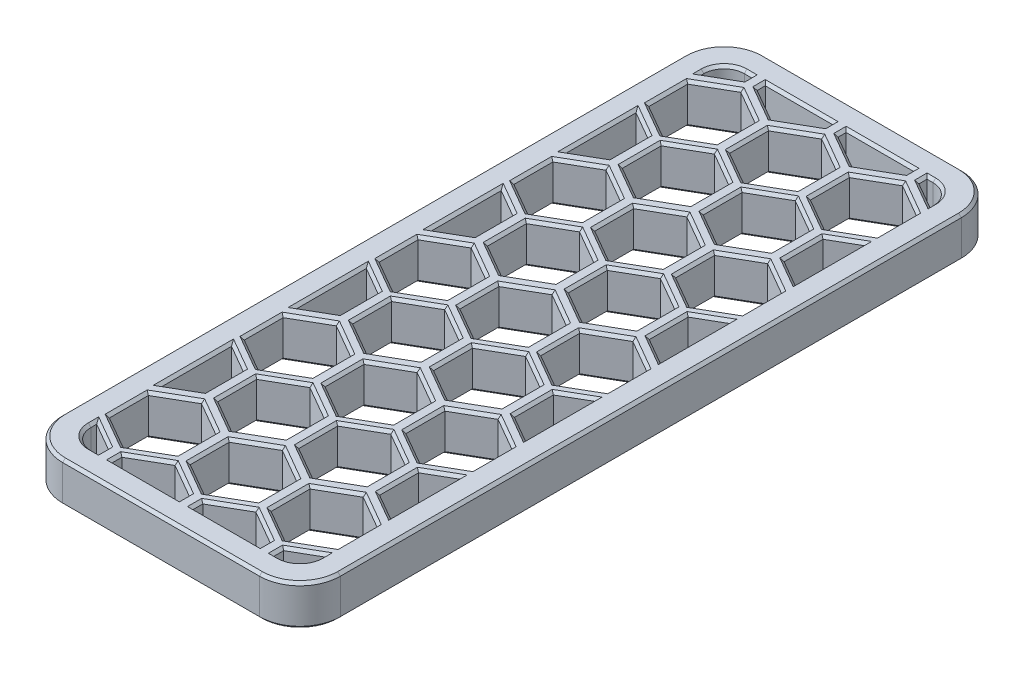
SolidWorks part; units mm, degrees
ref_plane "Front Plane" through (0, 0, 0) normal (0, 0, 1) x (1, 0, 0)
ref_plane "Top Plane" through (0, 0, 0) normal (0, 1, 0) x (1, 0, 0)
ref_plane "Right Plane" through (0, 0, 0) normal (1, 0, 0) x (0, 0, -1)
sketch "Sketch1" plane through (0, 0, 0) normal (0, 1, 0) x (1, 0, 0)
  line L1 (-68.5, 30) -> (68.5, 30)
  line L2 (-68.5, 30) -> (-68.5, -30)
  line L3 (-68.5, -30) -> (68.5, -30)
  line L4 (68.5, 30) -> (68.5, -30)
  line L5 (-68.5, 30) -> (68.5, -30) construction
  line L6 (-68.5, -30) -> (68.5, 30) construction
  point P0 (0, 0)
  dimension "D1" = 60
  dimension "D2" = 137
extrude "Boss-Extrude1" add sketch "Sketch1" along normal blind 6.5
sketch "Sketch2" plane through (0, 6.5, 0) normal (0, 1, 0) x (1, 0, 0)
  line L0 (0, 0) -> (47.9381, 0) construction
  line L1 (68.5, -30) -> (68.5, 30) construction
  line L2 (-36.5, 27.75) -> (64.5, 27.75)
  line L3 (-36.5, 27.75) -> (-36.5, -27.75)
  line L4 (-36.5, -27.75) -> (64.5, -27.75)
  line L5 (64.5, 27.75) -> (64.5, -27.75)
  line L6 (-36.5, 27.75) -> (64.5, -27.75) construction
  line L7 (-36.5, -27.75) -> (64.5, 27.75) construction
  point P3 (14, 0)
  dimension "D1" = 55.5
  dimension "D2" = 101
  dimension "D3" = 4
extrude "Cut-Extrude1" cut sketch "Sketch2" against normal blind 1.65
sketch "Sketch3" plane through (0, 4.85, 0) normal (0, 1, 0) x (1, 0, 0)
  line L0 (64.5, -27.75) -> (64.5, 27.75) construction
  line L1 (57.35, -27.75) -> (-29.95, -27.75)
  line L2 (57.35, -27.75) -> (57.35, 27.75)
  line L3 (57.35, 27.75) -> (-29.95, 27.75)
  line L4 (-29.95, -27.75) -> (-29.95, 27.75)
  line L5 (64.5, 27.75) -> (-36.5, 27.75) construction
  dimension "D1" = 7.15
  dimension "D2" = 87.3
  dimension "D3" = 55.5
  dimension "D4" = 0
extrude "Cut-Extrude2" cut sketch "Sketch3" against normal blind 4.1
sketch "Sketch4" plane through (0, 0.75, 0) normal (0, 1, 0) x (1, 0, 0)
  line L0 (0, 0) -> (36.8123, 0) construction
  line L1 (64.5, -27.75) -> (64.5, 27.75) construction
  line L2 (-20.6, 25.85) -> (54.8, 25.85)
  line L3 (-20.6, 25.85) -> (-20.6, -25.85)
  line L4 (-20.6, -25.85) -> (54.8, -25.85)
  line L5 (54.8, 25.85) -> (54.8, -25.85)
  line L6 (-20.6, 25.85) -> (54.8, -25.85) construction
  line L7 (-20.6, -25.85) -> (54.8, 25.85) construction
  point P3 (17.1, 0)
  dimension "D1" = 51.7
  dimension "D2" = 75.4
  dimension "D3" = 9.7
extrude "Cut-Extrude3" cut sketch "Sketch4" against normal through all
fillet "Fillet1" radius 1 4 edges at (54.8, 0.375, -25.85) (54.8, 0.375, 25.85) (-20.6, 0.375, 25.85) (-20.6, 0.375, -25.85)
sketch "Sketch6" plane through (0, 4.85, 0) normal (0, 1, 0) x (1, 0, 0)
  line L0 (57.35, -27.75) -> (57.35, 27.75) construction
  line L1 (64.5, -27.75) -> (57.35, -27.75)
  line L2 (64.5, -27.75) -> (64.5, -19.75)
  line L3 (64.5, -19.75) -> (57.35, -19.75)
  line L4 (57.35, -27.75) -> (57.35, -19.75)
  line L5 (57.35, -27.75) -> (57.35, 27.75) construction
  line L6 (64.5, 27.75) -> (57.35, 27.75)
  line L7 (64.5, 27.75) -> (64.5, 19.75)
  line L8 (64.5, 19.75) -> (57.35, 19.75)
  line L9 (57.35, 27.75) -> (57.35, 19.75)
  line L10 (-29.95, 27.75) -> (-29.95, -27.75) construction
  line L11 (-36.5, 27.75) -> (-29.95, 27.75)
  line L12 (-36.5, 27.75) -> (-36.5, 19.75)
  line L13 (-36.5, 19.75) -> (-29.95, 19.75)
  line L14 (-29.95, 27.75) -> (-29.95, 19.75)
  line L16 (-36.5, -27.75) -> (-29.95, -27.75)
  line L17 (-36.5, -27.75) -> (-36.5, -19.75)
  line L18 (-36.5, -19.75) -> (-29.95, -19.75)
  line L19 (-29.95, -27.75) -> (-29.95, -19.75)
  dimension "D1" = 8
  dimension "D2" = 8
  dimension "D3" = 8
  dimension "D4" = 8
extrude "Cut-Extrude4" cut sketch "Sketch6" against normal blind 2.5
fillet "Fillet2" radius 3 4 edges at (57.35, 3.6, -19.75) (57.35, 3.6, 19.75) (-29.95, 3.6, 19.75) (-29.95, 3.6, -19.75)
chamfer "Chamfer1" distance 0.5 angle 45 8 edges at (17.1, 0, -25.85) (-20.3071, 0, -25.5571) (54.5071, 0, -25.5571) (-20.6, 0, 0) (54.8, 0, 0) (-20.3071, 0, 25.5571) (54.5071, 0, 25.5571) (17.1, 0, 25.85)
sketch "Sketch7" plane through (0, 6.5, 0) normal (0, 1, 0) x (1, 0, 0)
  line L0 (0, 0) -> (-52.5, 0) construction
  line L1 (-36.5, 27.75) -> (-36.5, -27.75) construction
  line L2 (-63, 26.2268) -> (-42, 26.2268)
  line L3 (-63, 26.2268) -> (-63, -26.2268)
  line L4 (-63, -26.2268) -> (-42, -26.2268)
  line L5 (-42, 26.2268) -> (-42, -26.2268)
  line L6 (-63, 26.2268) -> (-42, -26.2268) construction
  line L7 (-63, -26.2268) -> (-42, 26.2268) construction
  line L8 (-68.5, 30) -> (-68.5, -30) construction
  dimension "D1" = 5.5
  dimension "D2" = 5.5
extrude "Cut-Extrude5" cut sketch "Sketch7" against normal through all
fillet "Fillet3" radius 3 4 edges at (-42, 3.25, 26.2268) (-63, 3.25, 26.2268) (-63, 3.25, -26.2268) (-42, 3.25, -26.2268)
fillet "Fillet5" radius 2 10 edges at (62.425, 4.85, 19.75) (58.2287, 4.85, 18.8713) (62.425, 4.85, -19.75) (58.2287, 4.85, -18.8713) (-34.725, 4.85, -19.75) (-30.8287, 4.85, -18.8713) (-34.725, 4.85, 19.75) (-30.8287, 4.85, 18.8713) (57.35, 4.85, 0) (-29.95, 4.85, 0)
chamfer "Chamfer3" distance 1 angle 45 4 edges at (57.35, 2.35, -22.25) (57.35, 2.35, 22.25) (-29.95, 2.35, 22.25) (-29.95, 2.35, -22.25)
fillet "Fillet6" radius 1.5 4 edges at (68.5, 3.25, 30) (-68.5, 3.25, 30) (-68.5, 3.25, -30) (68.5, 3.25, -30)
fillet "Fillet7" radius 1 16 edges at (-68.0607, 0, 29.5607) (-68.5, 0, 0) (-68.0607, 0, -29.5607) (0, 0, -30) (68.0607, 0, -29.5607) (68.5, 0, 0) (68.0607, 0, 29.5607) (-62.1213, 0, -25.3481) (-52.5, 0, -26.2268) (-42.8787, 0, -25.3481) (-42, 0, 0) (-42.8787, 0, 25.3481) (-52.5, 0, 26.2268) (-62.1213, 0, 25.3481) (0, 0, 30) (-63, 0, 0)
sketch "Sketch8" plane through (0, 0, 0) normal (0, -1, 0) x (1, 0, 0)
  line L28 (-45, 26.0268) -> (-60, 26.0268)
  line L29 (-42.2, -23.2268) -> (-42.2, 23.2268)
  line L30 (-60, -26.0268) -> (-45, -26.0268)
  line L31 (-62.8, 23.2268) -> (-62.8, -23.2268)
  line L32 (-45, 26.0268) -> (-60, 26.0268)
  line L33 (-42.2, -23.2268) -> (-42.2, 23.2268)
  line L34 (-60, -26.0268) -> (-45, -26.0268)
  line L35 (-62.8, 23.2268) -> (-62.8, -23.2268)
  arc A24 (-60, 26.0268) -> (-62.8, 23.2268) centre (-60, 23.2268) ccw
  arc A25 (-42.2, 23.2268) -> (-45, 26.0268) centre (-45, 23.2268) ccw
  arc A26 (-45, -26.0268) -> (-42.2, -23.2268) centre (-45, -23.2268) ccw
  arc A27 (-62.8, -23.2268) -> (-60, -26.0268) centre (-60, -23.2268) ccw
  arc A28 (-60, 26.0268) -> (-62.8, 23.2268) centre (-60, 23.2268) ccw
  arc A29 (-42.2, 23.2268) -> (-45, 26.0268) centre (-45, 23.2268) ccw
  arc A30 (-45, -26.0268) -> (-42.2, -23.2268) centre (-45, -23.2268) ccw
  arc A31 (-62.8, -23.2268) -> (-60, -26.0268) centre (-60, -23.2268) ccw
  dimension "D1" = 0.2
extrude "Boss-Extrude2" add sketch "Sketch8" along normal blind 10 separate body
sketch "Sketch9" plane through (-62.8, 0, 0) normal (-1, 0, 0) x (0, 0, 1)
  line L0 (23.2268, -10) -> (-23.2268, -10) construction
  line L1 (-34.3894, 13.8504) -> (38.8639, 13.8504)
  line L2 (-34.3894, 13.8504) -> (-34.3894, -7)
  line L3 (-34.3894, -7) -> (38.8639, -7)
  line L4 (38.8639, 13.8504) -> (38.8639, -7)
  dimension "D1" = 3
extrude "Cut-Extrude6" cut sketch "Sketch9" against normal through all and the other way through all
sketch "Sketch10" plane through (0, -10, 0) normal (0, -1, 0) x (1, 0, 0)
  line L0 (-52.4279, 17.1053) -> (-49.9279, 18.5487)
  line L1 (-58.4279, 17.1006) -> (-55.9279, 18.544)
  line L2 (-55.9279, 18.544) -> (-55.9279, 21.4307)
  line L3 (-55.9279, 21.4307) -> (-58.4279, 22.8741)
  line L4 (-58.4279, 22.8741) -> (-60.9279, 21.4307)
  line L5 (-60.9279, 21.4307) -> (-60.9279, 18.544)
  line L6 (-60.9279, 18.544) -> (-58.4279, 17.1006)
  line L7 (-49.9279, 18.5487) -> (-49.9279, 21.4354)
  line L8 (-49.9279, 21.4354) -> (-52.4279, 22.8788)
  line L9 (-52.4279, 22.8788) -> (-54.9279, 21.4354)
  line L10 (-54.9279, 21.4354) -> (-54.9279, 18.5487)
  line L11 (-54.9279, 18.5487) -> (-52.4279, 17.1053)
  line L12 (-46.4279, 17.1086) -> (-43.9279, 18.552)
  line L13 (-43.9279, 18.552) -> (-43.9279, 21.4387)
  line L14 (-43.9279, 21.4387) -> (-46.4279, 22.8821)
  line L15 (-46.4279, 22.8821) -> (-48.9279, 21.4387)
  line L16 (-48.9279, 21.4387) -> (-48.9279, 18.552)
  line L17 (-48.9279, 18.552) -> (-46.4279, 17.1086)
  line L18 (-58.4279, 7.1006) -> (-55.9279, 8.544)
  line L19 (-55.9279, 8.544) -> (-55.9279, 11.4307)
  line L20 (-55.4437, 12.0459) -> (-52.9437, 13.4893)
  line L21 (-52.9437, 13.4893) -> (-52.9437, 16.376)
  line L22 (-52.9437, 16.376) -> (-55.4437, 17.8194)
  line L23 (-55.4437, 17.8194) -> (-57.9437, 16.376)
  line L24 (-57.9437, 16.376) -> (-57.9437, 13.4893)
  line L25 (-57.9437, 13.4893) -> (-55.4437, 12.0459)
  line L26 (-55.9279, 11.4307) -> (-58.4279, 12.8741)
  line L27 (-58.4279, 12.8741) -> (-60.9279, 11.4307)
  line L28 (-60.9279, 11.4307) -> (-60.9279, 8.544)
  line L29 (-60.9279, 8.544) -> (-58.4279, 7.1006)
  line L30 (-52.4279, 7.1053) -> (-49.9279, 8.5487)
  line L31 (-49.9279, 8.5487) -> (-49.9279, 11.4354)
  line L32 (-49.9279, 11.4354) -> (-52.4279, 12.8788)
  line L33 (-52.4279, 12.8788) -> (-54.9279, 11.4354)
  line L34 (-54.9279, 11.4354) -> (-54.9279, 8.5487)
  line L35 (-54.9279, 8.5487) -> (-52.4279, 7.1053)
  line L36 (-46.4279, 7.1086) -> (-43.9279, 8.552)
  line L37 (-43.9279, 8.552) -> (-43.9279, 11.4387)
  line L38 (-43.9279, 11.4387) -> (-46.4279, 12.8821)
  line L39 (-46.4279, 12.8821) -> (-48.9279, 11.4387)
  line L40 (-48.9279, 11.4387) -> (-48.9279, 8.552)
  line L41 (-48.9279, 8.552) -> (-46.4279, 7.1086)
  line L42 (-58.4279, -2.8994) -> (-55.9279, -1.456)
  line L43 (-55.9279, -1.456) -> (-55.9279, 1.4307)
  line L44 (-55.9279, 1.4307) -> (-58.4279, 2.8741)
  line L45 (-58.4279, 2.8741) -> (-60.9279, 1.4307)
  line L46 (-60.9279, 1.4307) -> (-60.9279, -1.456)
  line L47 (-60.9279, -1.456) -> (-58.4279, -2.8994)
  line L48 (-52.4279, -2.8947) -> (-49.9279, -1.4513)
  line L49 (-49.9279, -1.4513) -> (-49.9279, 1.4354)
  line L50 (-49.9279, 1.4354) -> (-52.4279, 2.8788)
  line L51 (-52.4279, 2.8788) -> (-54.9279, 1.4354)
  line L52 (-54.9279, 1.4354) -> (-54.9279, -1.4513)
  line L53 (-54.9279, -1.4513) -> (-52.4279, -2.8947)
  line L54 (-46.4279, -2.8914) -> (-43.9279, -1.448)
  line L55 (-43.9279, -1.448) -> (-43.9279, 1.4387)
  line L56 (-43.9279, 1.4387) -> (-46.4279, 2.8821)
  line L57 (-46.4279, 2.8821) -> (-48.9279, 1.4387)
  line L58 (-48.9279, 1.4387) -> (-48.9279, -1.448)
  line L59 (-48.9279, -1.448) -> (-46.4279, -2.8914)
  line L60 (-58.4279, -12.8994) -> (-55.9279, -11.456)
  line L61 (-55.9279, -11.456) -> (-55.9279, -8.5693)
  line L62 (-55.9279, -8.5693) -> (-58.4279, -7.1259)
  line L63 (-58.4279, -7.1259) -> (-60.9279, -8.5693)
  line L64 (-60.9279, -8.5693) -> (-60.9279, -11.456)
  line L65 (-60.9279, -11.456) -> (-58.4279, -12.8994)
  line L66 (-52.4279, -12.8947) -> (-49.9279, -11.4513)
  line L67 (-49.9279, -11.4513) -> (-49.9279, -8.5646)
  line L68 (-49.9279, -8.5646) -> (-52.4279, -7.1212)
  line L69 (-52.4279, -7.1212) -> (-54.9279, -8.5646)
  line L70 (-54.9279, -8.5646) -> (-54.9279, -11.4513)
  line L71 (-54.9279, -11.4513) -> (-52.4279, -12.8947)
  line L72 (-46.4279, -12.8914) -> (-43.9279, -11.448)
  line L73 (-43.9279, -11.448) -> (-43.9279, -8.5613)
  line L74 (-43.9279, -8.5613) -> (-46.4279, -7.1179)
  line L75 (-46.4279, -7.1179) -> (-48.9279, -8.5613)
  line L76 (-48.9279, -8.5613) -> (-48.9279, -11.448)
  line L77 (-48.9279, -11.448) -> (-46.4279, -12.8914)
  line L78 (-58.4279, -22.8994) -> (-55.9279, -21.456)
  line L79 (-55.9279, -21.456) -> (-55.9279, -18.5693)
  line L80 (-55.9279, -18.5693) -> (-58.4279, -17.1259)
  line L81 (-58.4279, -17.1259) -> (-60.9279, -18.5693)
  line L82 (-60.9279, -18.5693) -> (-60.9279, -21.456)
  line L83 (-60.9279, -21.456) -> (-58.4279, -22.8994)
  line L84 (-52.4279, -22.8947) -> (-49.9279, -21.4513)
  line L85 (-49.9279, -21.4513) -> (-49.9279, -18.5646)
  line L86 (-49.9279, -18.5646) -> (-52.4279, -17.1212)
  line L87 (-52.4279, -17.1212) -> (-54.9279, -18.5646)
  line L88 (-54.9279, -18.5646) -> (-54.9279, -21.4513)
  line L89 (-54.9279, -21.4513) -> (-52.4279, -22.8947)
  line L90 (-46.4279, -22.8914) -> (-43.9279, -21.448)
  line L91 (-43.9279, -21.448) -> (-43.9279, -18.5613)
  line L92 (-43.9279, -18.5613) -> (-46.4279, -17.1179)
  line L93 (-46.4279, -17.1179) -> (-48.9279, -18.5613)
  line L94 (-48.9279, -18.5613) -> (-48.9279, -21.448)
  line L95 (-48.9279, -21.448) -> (-46.4279, -22.8914)
  line L96 (-55.4437, 2.0459) -> (-52.9437, 3.4893)
  line L97 (-52.9437, 3.4893) -> (-52.9437, 6.376)
  line L98 (-52.9437, 6.376) -> (-55.4437, 7.8194)
  line L99 (-55.4437, 7.8194) -> (-57.9437, 6.376)
  line L100 (-57.9437, 6.376) -> (-57.9437, 3.4893)
  line L101 (-57.9437, 3.4893) -> (-55.4437, 2.0459)
  line L102 (-55.4437, -7.9541) -> (-52.9437, -6.5107)
  line L103 (-52.9437, -6.5107) -> (-52.9437, -3.624)
  line L104 (-52.9437, -3.624) -> (-55.4437, -2.1806)
  line L105 (-55.4437, -2.1806) -> (-57.9437, -3.624)
  line L106 (-57.9437, -3.624) -> (-57.9437, -6.5107)
  line L107 (-57.9437, -6.5107) -> (-55.4437, -7.9541)
  line L108 (-55.4437, -17.9541) -> (-52.9437, -16.5107)
  line L109 (-52.9437, -16.5107) -> (-52.9437, -13.624)
  line L110 (-52.9437, -13.624) -> (-55.4437, -12.1806)
  line L111 (-55.4437, -12.1806) -> (-57.9437, -13.624)
  line L112 (-57.9437, -13.624) -> (-57.9437, -16.5107)
  line L113 (-57.9437, -16.5107) -> (-55.4437, -17.9541)
  line L114 (-55.4437, -27.9541) -> (-52.9437, -26.5107)
  line L115 (-52.9437, -26.5107) -> (-52.9437, -23.624)
  line L116 (-52.9437, -23.624) -> (-55.4437, -22.1806)
  line L117 (-55.4437, -22.1806) -> (-57.9437, -23.624)
  line L118 (-57.9437, -23.624) -> (-57.9437, -26.5107)
  line L119 (-57.9437, -26.5107) -> (-55.4437, -27.9541)
  line L120 (-55.4437, 12.0459) -> (-52.9437, 13.4893)
  line L121 (-52.9437, 13.4893) -> (-52.9437, 16.376)
  line L122 (-52.9437, 16.376) -> (-55.4437, 17.8194)
  line L123 (-55.4437, 17.8194) -> (-57.9437, 16.376)
  line L124 (-57.9437, 16.376) -> (-57.9437, 13.4893)
  line L125 (-57.9437, 13.4893) -> (-55.4437, 12.0459)
  line L126 (-55.4437, 2.0459) -> (-52.9437, 3.4893)
  line L127 (-52.9437, 3.4893) -> (-52.9437, 6.376)
  line L128 (-52.9437, 6.376) -> (-55.4437, 7.8194)
  line L129 (-55.4437, 7.8194) -> (-57.9437, 6.376)
  line L130 (-57.9437, 6.376) -> (-57.9437, 3.4893)
  line L131 (-57.9437, 3.4893) -> (-55.4437, 2.0459)
  line L132 (-55.4437, -7.9541) -> (-52.9437, -6.5107)
  line L133 (-52.9437, -6.5107) -> (-52.9437, -3.624)
  line L134 (-52.9437, -3.624) -> (-55.4437, -2.1806)
  line L135 (-55.4437, -2.1806) -> (-57.9437, -3.624)
  line L136 (-57.9437, -3.624) -> (-57.9437, -6.5107)
  line L137 (-57.9437, -6.5107) -> (-55.4437, -7.9541)
  line L138 (-55.4437, -17.9541) -> (-52.9437, -16.5107)
  line L139 (-52.9437, -16.5107) -> (-52.9437, -13.624)
  line L140 (-52.9437, -13.624) -> (-55.4437, -12.1806)
  line L141 (-55.4437, -12.1806) -> (-57.9437, -13.624)
  line L142 (-57.9437, -13.624) -> (-57.9437, -16.5107)
  line L143 (-57.9437, -16.5107) -> (-55.4437, -17.9541)
  line L144 (-55.4437, 22.0459) -> (-52.9437, 23.4893)
  line L145 (-52.9437, 23.4893) -> (-52.9437, 26.376)
  line L146 (-52.9437, 26.376) -> (-55.4437, 27.8194)
  line L147 (-55.4437, 27.8194) -> (-57.9437, 26.376)
  line L148 (-57.9437, 26.376) -> (-57.9437, 23.4893)
  line L149 (-57.9437, 23.4893) -> (-55.4437, 22.0459)
  line L150 (-49.4437, 22.0459) -> (-46.9437, 23.4893)
  line L151 (-46.9437, 23.4893) -> (-46.9437, 26.376)
  line L152 (-46.9437, 26.376) -> (-49.4437, 27.8194)
  line L153 (-49.4437, 27.8194) -> (-51.9437, 26.376)
  line L154 (-51.9437, 26.376) -> (-51.9437, 23.4893)
  line L155 (-51.9437, 23.4893) -> (-49.4437, 22.0459)
  line L156 (-49.4437, 12.0459) -> (-46.9437, 13.4893)
  line L157 (-46.9437, 13.4893) -> (-46.9437, 16.376)
  line L158 (-46.9437, 16.376) -> (-49.4437, 17.8194)
  line L159 (-49.4437, 17.8194) -> (-51.9437, 16.376)
  line L160 (-51.9437, 16.376) -> (-51.9437, 13.4893)
  line L161 (-51.9437, 13.4893) -> (-49.4437, 12.0459)
  line L162 (-49.4437, 2.0459) -> (-46.9437, 3.4893)
  line L163 (-46.9437, 3.4893) -> (-46.9437, 6.376)
  line L164 (-46.9437, 6.376) -> (-49.4437, 7.8194)
  line L165 (-49.4437, 7.8194) -> (-51.9437, 6.376)
  line L166 (-51.9437, 6.376) -> (-51.9437, 3.4893)
  line L167 (-51.9437, 3.4893) -> (-49.4437, 2.0459)
  line L168 (-49.4437, -7.9541) -> (-46.9437, -6.5107)
  line L169 (-46.9437, -6.5107) -> (-46.9437, -3.624)
  line L170 (-46.9437, -3.624) -> (-49.4437, -2.1806)
  line L171 (-49.4437, -2.1806) -> (-51.9437, -3.624)
  line L172 (-51.9437, -3.624) -> (-51.9437, -6.5107)
  line L173 (-51.9437, -6.5107) -> (-49.4437, -7.9541)
  line L174 (-49.4437, -17.9541) -> (-46.9437, -16.5107)
  line L175 (-46.9437, -16.5107) -> (-46.9437, -13.624)
  line L176 (-46.9437, -13.624) -> (-49.4437, -12.1806)
  line L177 (-49.4437, -12.1806) -> (-51.9437, -13.624)
  line L178 (-51.9437, -13.624) -> (-51.9437, -16.5107)
  line L179 (-51.9437, -16.5107) -> (-49.4437, -17.9541)
  line L180 (-49.4437, -27.9541) -> (-46.9437, -26.5107)
  line L181 (-46.9437, -26.5107) -> (-46.9437, -23.624)
  line L182 (-46.9437, -23.624) -> (-49.4437, -22.1806)
  line L183 (-49.4437, -22.1806) -> (-51.9437, -23.624)
  line L184 (-51.9437, -23.624) -> (-51.9437, -26.5107)
  line L185 (-51.9437, -26.5107) -> (-49.4437, -27.9541)
  line L186 (-43.4437, 22.0459) -> (-40.9437, 23.4893)
  line L187 (-40.9437, 23.4893) -> (-40.9437, 26.376)
  line L188 (-40.9437, 26.376) -> (-43.4437, 27.8194)
  line L189 (-43.4437, 27.8194) -> (-45.9437, 26.376)
  line L190 (-45.9437, 26.376) -> (-45.9437, 23.4893)
  line L191 (-45.9437, 23.4893) -> (-43.4437, 22.0459)
  line L192 (-43.4437, 12.0459) -> (-40.9437, 13.4893)
  line L193 (-40.9437, 13.4893) -> (-40.9437, 16.376)
  line L194 (-40.9437, 16.376) -> (-43.4437, 17.8194)
  line L195 (-43.4437, 17.8194) -> (-45.9437, 16.376)
  line L196 (-45.9437, 16.376) -> (-45.9437, 13.4893)
  line L197 (-45.9437, 13.4893) -> (-43.4437, 12.0459)
  line L198 (-43.4437, 2.0459) -> (-40.9437, 3.4893)
  line L199 (-40.9437, 3.4893) -> (-40.9437, 6.376)
  line L200 (-40.9437, 6.376) -> (-43.4437, 7.8194)
  line L201 (-43.4437, 7.8194) -> (-45.9437, 6.376)
  line L202 (-45.9437, 6.376) -> (-45.9437, 3.4893)
  line L203 (-45.9437, 3.4893) -> (-43.4437, 2.0459)
  line L204 (-43.4437, -7.9541) -> (-40.9437, -6.5107)
  line L205 (-40.9437, -6.5107) -> (-40.9437, -3.624)
  line L206 (-40.9437, -3.624) -> (-43.4437, -2.1806)
  line L207 (-43.4437, -2.1806) -> (-45.9437, -3.624)
  line L208 (-45.9437, -3.624) -> (-45.9437, -6.5107)
  line L209 (-45.9437, -6.5107) -> (-43.4437, -7.9541)
  line L210 (-43.4437, -17.9541) -> (-40.9437, -16.5107)
  line L211 (-40.9437, -16.5107) -> (-40.9437, -13.624)
  line L212 (-40.9437, -13.624) -> (-43.4437, -12.1806)
  line L213 (-43.4437, -12.1806) -> (-45.9437, -13.624)
  line L214 (-45.9437, -13.624) -> (-45.9437, -16.5107)
  line L215 (-45.9437, -16.5107) -> (-43.4437, -17.9541)
  line L216 (-43.4437, -27.9541) -> (-40.9437, -26.5107)
  line L217 (-40.9437, -26.5107) -> (-40.9437, -23.624)
  line L218 (-40.9437, -23.624) -> (-43.4437, -22.1806)
  line L219 (-43.4437, -22.1806) -> (-45.9437, -23.624)
  line L220 (-45.9437, -23.624) -> (-45.9437, -26.5107)
  line L221 (-45.9437, -26.5107) -> (-43.4437, -27.9541)
  line L222 (-61.4437, 22.0459) -> (-58.9437, 23.4893)
  line L223 (-58.9437, 23.4893) -> (-58.9437, 26.376)
  line L224 (-58.9437, 26.376) -> (-61.4437, 27.8194)
  line L225 (-61.4437, 27.8194) -> (-63.9437, 26.376)
  line L226 (-63.9437, 26.376) -> (-63.9437, 23.4893)
  line L227 (-63.9437, 23.4893) -> (-61.4437, 22.0459)
  line L228 (-61.4437, 12.0459) -> (-58.9437, 13.4893)
  line L229 (-58.9437, 13.4893) -> (-58.9437, 16.376)
  line L230 (-58.9437, 16.376) -> (-61.4437, 17.8194)
  line L231 (-61.4437, 17.8194) -> (-63.9437, 16.376)
  line L232 (-63.9437, 16.376) -> (-63.9437, 13.4893)
  line L233 (-63.9437, 13.4893) -> (-61.4437, 12.0459)
  line L234 (-61.4437, 2.0459) -> (-58.9437, 3.4893)
  line L235 (-58.9437, 3.4893) -> (-58.9437, 6.376)
  line L236 (-58.9437, 6.376) -> (-61.4437, 7.8194)
  line L237 (-61.4437, 7.8194) -> (-63.9437, 6.376)
  line L238 (-63.9437, 6.376) -> (-63.9437, 3.4893)
  line L239 (-63.9437, 3.4893) -> (-61.4437, 2.0459)
  line L240 (-61.4437, -7.9541) -> (-58.9437, -6.5107)
  line L241 (-58.9437, -6.5107) -> (-58.9437, -3.624)
  line L242 (-58.9437, -3.624) -> (-61.4437, -2.1806)
  line L243 (-61.4437, -2.1806) -> (-63.9437, -3.624)
  line L244 (-63.9437, -3.624) -> (-63.9437, -6.5107)
  line L245 (-63.9437, -6.5107) -> (-61.4437, -7.9541)
  line L246 (-61.4437, -17.9541) -> (-58.9437, -16.5107)
  line L247 (-58.9437, -16.5107) -> (-58.9437, -13.624)
  line L248 (-58.9437, -13.624) -> (-61.4437, -12.1806)
  line L249 (-61.4437, -12.1806) -> (-63.9437, -13.624)
  line L250 (-63.9437, -13.624) -> (-63.9437, -16.5107)
  line L251 (-63.9437, -16.5107) -> (-61.4437, -17.9541)
  line L252 (-61.4437, -27.9541) -> (-58.9437, -26.5107)
  line L253 (-58.9437, -26.5107) -> (-58.9437, -23.624)
  line L254 (-58.9437, -23.624) -> (-61.4437, -22.1806)
  line L255 (-61.4437, -22.1806) -> (-63.9437, -23.624)
  line L256 (-63.9437, -23.624) -> (-63.9437, -26.5107)
  line L257 (-63.9437, -26.5107) -> (-61.4437, -27.9541)
  circle A0 centre (-58.4279, 19.9873) radius 2.5 construction
  circle A1 centre (-52.4279, 19.992) radius 2.5 construction
  circle A2 centre (-46.4279, 19.9954) radius 2.5 construction
  circle A3 centre (-55.4437, 14.9326) radius 2.5 construction
  point P105 (0, 0)
  point P231 (0, 0)
  point P268 (0, 0)
  point P269 (-57.9437, 26.376)
  point P270 (-57.9437, 26.376)
  point P271 (0, 0)
  point P272 (0, 0)
  arc M259 (-60, 26.0268) -> (-62.8, 23.2268) centre (-60, 23.2268) ccw
  line M260 (-62.8, 23.2268) -> (-62.8, -23.2268)
  arc M261 (-62.8, -23.2268) -> (-60, -26.0268) centre (-60, -23.2268) ccw
  line M262 (-60, -26.0268) -> (-45, -26.0268)
  arc M263 (-45, -26.0268) -> (-42.2, -23.2268) centre (-45, -23.2268) ccw
  line M264 (-42.2, -23.2268) -> (-42.2, 23.2268)
  arc M265 (-42.2, 23.2268) -> (-45, 26.0268) centre (-45, 23.2268) ccw
  line M266 (-45, 26.0268) -> (-60, 26.0268)
  dimension "D1" = 5
  dimension "D2" = 5
  dimension "D3" = 1
  dimension "D4" = 5
  dimension "D5" = 1
  dimension "D6" = 5
  dimension "D7" = 5
  dimension "D8" = 5
  dimension "D9" = 2
  dimension "D10" = 3
  dimension "D11" = 2
extrude "Cut-Extrude7" cut sketch "Sketch10" against normal through all contours L226 L227 L223 L224 L225 M260 M259 M266 | L147 L148 L145 L146 M266 | L148 L149 L144 L145 M266 | L227 L222 L223 M260 M266 M259 | L154 L155 L150 L151 M266 | L190 L191 L186 M264 M265 M266 | L189 L190 L186 L187 L188 M266 M265 M264 | L153 L154 L151 L152 M266 | L16 L17 L12 L13 L14 L15 | L10 L11 L0 L7 L8 L9 | L5 L6 L1 L2 L3 L4 | L233 L228 L229 L230 L231 M260 | L232 L233 L231 M260 | L24 L25 L20 L21 L22 L23 | L160 L161 L156 L157 L158 L159 | L196 L197 L192 L194 L195 M264 | L193 L194 L192 M264 | L40 L41 L36 L37 L38 L39 | L34 L35 L30 L31 L32 L33 | L28 L29 L18 L19 L26 L27 | L239 L234 L235 L236 L237 M260 | L238 L239 L237 M260 | L244 L245 L243 M260 | L245 L240 L241 L242 L243 M260 | L46 L47 L42 L43 L44 L45 | L100 L101 L96 L97 L98 L99 | L166 L167 L162 L163 L164 L165 | L202 L203 L198 L200 L201 M264 | L199 L200 L198 M264 | L208 L209 L204 L206 L207 M264 | L205 L206 L204 M264 | L58 L59 L54 L55 L56 L57 | L52 L53 L48 L49 L50 L51 | L106 L107 L102 L103 L104 L105 | L172 L173 L168 L169 L170 L171 | L76 L77 L72 L73 L74 L75 | L70 L71 L66 L67 L68 L69 | L64 L65 L60 L61 L62 L63 | L251 L246 L247 L248 L249 M260 | L250 L251 L249 M260 | L256 L257 L252 L253 L255 M262 M261 M260 | L254 L255 L253 M260 M261 M262 | L82 L83 L78 L79 L80 L81 | L117 L118 L115 L116 M262 | L118 L119 L114 L115 M262 | L112 L113 L108 L109 L110 L111 | L88 L89 L84 L85 L86 L87 | L178 L179 L174 L175 L176 L177 | L94 L95 L90 L91 L92 L93 | L214 L215 L210 L212 L213 M264 | L211 L212 L210 M264 | L220 L221 L216 L217 L218 M264 M263 M262 | L219 L220 L218 M262 M263 M264 | L183 L184 L181 L182 M262 | L184 L185 L180 L181 M262
sketch "Sketch12" plane through (0, -10, 0) normal (0, -1, 0) x (1, 0, 0)
  line L1 (-59.8, 26.0268) -> (-45.2, 26.0268)
  line L2 (-62.8, 23.0268) -> (-62.8, -23.0268)
  line L3 (-59.8, -26.0268) -> (-45.2, -26.0268)
  line L4 (-42.2, 23.0268) -> (-42.2, -23.0268)
  line L5 (-59.5, 24.2268) -> (-45.5, 24.2268)
  line L6 (-61, 22.7268) -> (-61, -22.7268)
  line L7 (-59.5, -24.2268) -> (-45.5, -24.2268)
  line L8 (-44, 22.7268) -> (-44, -22.7268)
  arc A0 (-62.8, -23.0268) -> (-59.8, -26.0268) centre (-59.8, -23.0268) ccw
  arc A1 (-45.2, -26.0268) -> (-42.2, -23.0268) centre (-45.2, -23.0268) ccw
  arc A2 (-45.2, 26.0268) -> (-42.2, 23.0268) centre (-45.2, 23.0268) cw
  arc A3 (-59.8, 26.0268) -> (-62.8, 23.0268) centre (-59.8, 23.0268) ccw
  arc A4 (-61, -22.7268) -> (-59.5, -24.2268) centre (-59.5, -22.7268) ccw
  arc A5 (-45.5, -24.2268) -> (-44, -22.7268) centre (-45.5, -22.7268) ccw
  arc A6 (-59.5, 24.2268) -> (-61, 22.7268) centre (-59.5, 22.7268) ccw
  arc A7 (-45.5, 24.2268) -> (-44, 22.7268) centre (-45.5, 22.7268) cw
  dimension "D1" = 3
  dimension "D6" = 1.5
  dimension "D2" = 1.8
  dimension "D3" = 1.8
  dimension "D4" = 1.8
  dimension "D5" = 1.8
extrude "Boss-Extrude3" add sketch "Sketch12" against normal up to surface (3 mm away) up to face at (-46.4279, -7, -0.0046)
chamfer "Chamfer4" distance 0.2 angle 45 218 edges at (-53.6779, -10, -22.173) (-51.1779, -10, -22.173) (-49.9279, -10, -20.008) (-51.1779, -10, -17.8429) (-53.6779, -10, -17.8429) (-54.9279, -10, -20.008) (-50.6937, -10, -17.2324) (-48.1937, -10, -17.2324) (-46.9437, -10, -15.0674) (-48.1937, -10, -12.9023) (-50.6937, -10, -12.9023) (-51.9437, -10, -15.0674) (-59.6779, -10, 7.8223) (-57.1779, -10, 7.8223) (-55.9279, -10, 9.9873) (-57.1779, -10, 12.1524) (-59.6779, -10, 12.1524) (-60.9279, -10, 9.9873) (-59.6779, -10, -2.1777) (-57.1779, -10, -2.1777) (-55.9279, -10, -0.0127) (-57.1779, -10, 2.1524) (-59.6779, -10, 2.1524) (-60.9279, -10, -0.0127) (-50.6937, -10, 12.7676) (-48.1937, -10, 12.7676) (-46.9437, -10, 14.9326) (-48.1937, -10, 17.0977) (-50.6937, -10, 17.0977) (-51.9437, -10, 14.9326) (-53.6779, -10, 7.827) (-51.1779, -10, 7.827) (-49.9279, -10, 9.992) (-51.1779, -10, 12.1571) (-53.6779, -10, 12.1571) (-54.9279, -10, 9.992) (-56.6937, -10, 12.7676) (-54.1937, -10, 12.7676) (-52.9437, -10, 14.9326) (-54.1937, -10, 17.0977) (-56.6937, -10, 17.0977) (-57.9437, -10, 14.9326) (-59.6779, -10, 17.8223) (-57.1779, -10, 17.8223) (-55.9279, -10, 19.9873) (-57.1779, -10, 22.1524) (-59.6779, -10, 22.1524) (-60.9279, -10, 19.9873) (-53.6779, -10, 17.827) (-51.1779, -10, 17.827) (-49.9279, -10, 19.992) (-51.1779, -10, 22.1571) (-53.6779, -10, 22.1571) (-54.9279, -10, 19.992) (-53.6779, -10, -12.173) (-51.1779, -10, -12.173) (-49.9279, -10, -10.008) (-51.1779, -10, -7.8429) (-53.6779, -10, -7.8429) (-54.9279, -10, -10.008) (-59.6779, -10, -12.1777) (-57.1779, -10, -12.1777) (-55.9279, -10, -10.0127) (-57.1779, -10, -7.8476) (-59.6779, -10, -7.8476) (-60.9279, -10, -10.0127) (-56.6937, -10, -17.2324) (-54.1937, -10, -17.2324) (-52.9437, -10, -15.0674) (-54.1937, -10, -12.9023) (-56.6937, -10, -12.9023) (-57.9437, -10, -15.0674) (-59.6779, -10, -22.1777) (-57.1779, -10, -22.1777) (-55.9279, -10, -20.0127) (-57.1779, -10, -17.8476) (-59.6779, -10, -17.8476) (-60.9279, -10, -20.0127) (-56.6937, -10, 2.7676) (-54.1937, -10, 2.7676) (-52.9437, -10, 4.9326) (-54.1937, -10, 7.0977) (-56.6937, -10, 7.0977) (-57.9437, -10, 4.9326) (-50.6937, -10, 2.7676) (-48.1937, -10, 2.7676) (-46.9437, -10, 4.9326) (-48.1937, -10, 7.0977) (-50.6937, -10, 7.0977) (-51.9437, -10, 4.9326) (-50.6937, -10, -7.2324) (-48.1937, -10, -7.2324) (-46.9437, -10, -5.0674) (-48.1937, -10, -2.9023) (-50.6937, -10, -2.9023) (-51.9437, -10, -5.0674) (-56.6937, -10, -7.2324) (-54.1937, -10, -7.2324) (-52.9437, -10, -5.0674) (-54.1937, -10, -2.9023) (-56.6937, -10, -2.9023) (-57.9437, -10, -5.0674) (-53.6779, -10, -2.173) (-51.1779, -10, -2.173) (-49.9279, -10, -0.008) (-51.1779, -10, 2.1571) (-53.6779, -10, 2.1571) (-54.9279, -10, -0.008) (-43.0787, -10, 25.1481) (-42.2, -10, 0) (-43.0787, -10, -25.1481) (-52.5, -10, -26.0268) (-61.9213, -10, -25.1481) (-62.8, -10, 0) (-61.9213, -10, 25.1481) (-52.5, -10, 26.0268) (-59.9718, -10, -23.0304) (-61, -10, -22.5818) (-60.5607, -10, -23.7875) (-59.2218, -10, -24.2268) (-58.9437, -10, -23.9254) (-59.9718, -10, -17.1043) (-58.9437, -10, -15.0674) (-59.9718, -10, -13.0304) (-61, -10, -15.0674) (-59.9718, -10, -7.1043) (-58.9437, -10, -5.0674) (-59.9718, -10, -3.0304) (-61, -10, -5.0674) (-59.9718, -10, 2.8957) (-58.9437, -10, 4.9326) (-59.9718, -10, 6.9696) (-61, -10, 4.9326) (-59.9718, -10, 12.8957) (-58.9437, -10, 14.9326) (-59.9718, -10, 16.9696) (-61, -10, 14.9326) (-60.5607, -10, 23.7875) (-61, -10, 22.5144) (-59.9718, -10, 22.8957) (-58.9437, -10, 23.858) (-59.2218, -10, 24.2268) (-57.9437, -10, 23.858) (-56.6937, -10, 22.7676) (-54.1937, -10, 22.7676) (-52.9437, -10, 23.858) (-55.4437, -10, 24.2268) (-51.9437, -10, 23.858) (-50.6937, -10, 22.7676) (-48.1937, -10, 22.7676) (-46.9437, -10, 23.858) (-49.4437, -10, 24.2268) (-44.4393, -10, 23.7875) (-45.7218, -10, 24.2268) (-45.9437, -10, 23.858) (-44.9718, -10, 22.9282) (-44, -10, 22.5469) (-45.214, -10, 22.1812) (-47.6779, -10, 22.1604) (-48.9279, -10, 19.9954) (-47.6779, -10, 17.8303) (-45.214, -10, 17.8095) (-44, -10, 19.9954) (-44.9718, -10, 16.9371) (-45.9437, -10, 14.9326) (-44.9718, -10, 12.9282) (-44, -10, 14.9326) (-45.214, -10, 12.1812) (-47.6779, -10, 12.1604) (-48.9279, -10, 9.9954) (-47.6779, -10, 7.8303) (-45.214, -10, 7.8095) (-44, -10, 9.9954) (-44.9718, -10, 6.9371) (-45.9437, -10, 4.9326) (-44.9718, -10, 2.9282) (-44, -10, 4.9326) (-45.214, -10, 2.1812) (-47.6779, -10, 2.1604) (-48.9279, -10, -0.0046) (-47.6779, -10, -2.1697) (-45.214, -10, -2.1905) (-44, -10, -0.0046) (-44.9718, -10, -3.0629) (-45.9437, -10, -5.0674) (-44.9718, -10, -7.0718) (-44, -10, -5.0674) (-45.214, -10, -7.8188) (-47.6779, -10, -7.8396) (-48.9279, -10, -10.0046) (-47.6779, -10, -12.1697) (-45.214, -10, -12.1905) (-44, -10, -10.0046) (-44.9718, -10, -13.0629) (-45.9437, -10, -15.0674) (-44.9718, -10, -17.0718) (-44, -10, -15.0674) (-45.214, -10, -17.8188) (-47.6779, -10, -17.8396) (-48.9279, -10, -20.0046) (-47.6779, -10, -22.1697) (-45.214, -10, -22.1905) (-44, -10, -20.0046) (-44.4393, -10, -23.7875) (-44, -10, -22.6143) (-44.9718, -10, -23.0629) (-45.9437, -10, -23.9254) (-45.7218, -10, -24.2268) (-46.9437, -10, -23.9254) (-48.1937, -10, -22.9023) (-50.6937, -10, -22.9023) (-51.9437, -10, -23.9254) (-49.4437, -10, -24.2268) (-52.9437, -10, -23.9254) (-54.1937, -10, -22.9023) (-56.6937, -10, -22.9023) (-57.9437, -10, -23.9254) (-55.4437, -10, -24.2268)
chamfer "Chamfer5" distance 0.2 angle 45 218 edges at (-51.1779, -7, -17.8429) (-49.9279, -7, -20.008) (-51.1779, -7, -22.173) (-53.6779, -7, -22.173) (-54.9279, -7, -20.008) (-53.6779, -7, -17.8429) (-48.1937, -7, -12.9023) (-46.9437, -7, -15.0674) (-48.1937, -7, -17.2324) (-50.6937, -7, -17.2324) (-51.9437, -7, -15.0674) (-50.6937, -7, -12.9023) (-57.1779, -7, 12.1524) (-55.9279, -7, 9.9873) (-57.1779, -7, 7.8223) (-59.6779, -7, 7.8223) (-60.9279, -7, 9.9873) (-59.6779, -7, 12.1524) (-57.1779, -7, 2.1524) (-55.9279, -7, -0.0127) (-57.1779, -7, -2.1777) (-59.6779, -7, -2.1777) (-60.9279, -7, -0.0127) (-59.6779, -7, 2.1524) (-48.1937, -7, 17.0977) (-46.9437, -7, 14.9326) (-48.1937, -7, 12.7676) (-50.6937, -7, 12.7676) (-51.9437, -7, 14.9326) (-50.6937, -7, 17.0977) (-51.1779, -7, 12.1571) (-49.9279, -7, 9.992) (-51.1779, -7, 7.827) (-53.6779, -7, 7.827) (-54.9279, -7, 9.992) (-53.6779, -7, 12.1571) (-54.1937, -7, 17.0977) (-52.9437, -7, 14.9326) (-54.1937, -7, 12.7676) (-56.6937, -7, 12.7676) (-57.9437, -7, 14.9326) (-56.6937, -7, 17.0977) (-57.1779, -7, 22.1524) (-55.9279, -7, 19.9873) (-57.1779, -7, 17.8223) (-59.6779, -7, 17.8223) (-60.9279, -7, 19.9873) (-59.6779, -7, 22.1524) (-51.1779, -7, 22.1571) (-49.9279, -7, 19.992) (-51.1779, -7, 17.827) (-53.6779, -7, 17.827) (-54.9279, -7, 19.992) (-53.6779, -7, 22.1571) (-51.1779, -7, -7.8429) (-49.9279, -7, -10.008) (-51.1779, -7, -12.173) (-53.6779, -7, -12.173) (-54.9279, -7, -10.008) (-53.6779, -7, -7.8429) (-57.1779, -7, -7.8476) (-55.9279, -7, -10.0127) (-57.1779, -7, -12.1777) (-59.6779, -7, -12.1777) (-60.9279, -7, -10.0127) (-59.6779, -7, -7.8476) (-54.1937, -7, -12.9023) (-52.9437, -7, -15.0674) (-54.1937, -7, -17.2324) (-56.6937, -7, -17.2324) (-57.9437, -7, -15.0674) (-56.6937, -7, -12.9023) (-57.1779, -7, -17.8476) (-55.9279, -7, -20.0127) (-57.1779, -7, -22.1777) (-59.6779, -7, -22.1777) (-60.9279, -7, -20.0127) (-59.6779, -7, -17.8476) (-54.1937, -7, 7.0977) (-52.9437, -7, 4.9326) (-54.1937, -7, 2.7676) (-56.6937, -7, 2.7676) (-57.9437, -7, 4.9326) (-56.6937, -7, 7.0977) (-48.1937, -7, 7.0977) (-46.9437, -7, 4.9326) (-48.1937, -7, 2.7676) (-50.6937, -7, 2.7676) (-51.9437, -7, 4.9326) (-50.6937, -7, 7.0977) (-48.1937, -7, -2.9023) (-46.9437, -7, -5.0674) (-48.1937, -7, -7.2324) (-50.6937, -7, -7.2324) (-51.9437, -7, -5.0674) (-50.6937, -7, -2.9023) (-54.1937, -7, -2.9023) (-52.9437, -7, -5.0674) (-54.1937, -7, -7.2324) (-56.6937, -7, -7.2324) (-57.9437, -7, -5.0674) (-56.6937, -7, -2.9023) (-51.1779, -7, 2.1571) (-49.9279, -7, -0.008) (-51.1779, -7, -2.173) (-53.6779, -7, -2.173) (-54.9279, -7, -0.008) (-53.6779, -7, 2.1571) (-62.8, -7, 0) (-61.9213, -7, -25.1481) (-52.5, -7, -26.0268) (-43.0787, -7, -25.1481) (-42.2, -7, 0) (-43.0787, -7, 25.1481) (-52.5, -7, 26.0268) (-61.9213, -7, 25.1481) (-60.5607, -7, -23.7875) (-61, -7, -22.5818) (-59.9718, -7, -23.0304) (-58.9437, -7, -23.9254) (-59.2218, -7, -24.2268) (-58.9437, -7, -15.0674) (-59.9718, -7, -17.1043) (-61, -7, -15.0674) (-59.9718, -7, -13.0304) (-58.9437, -7, -5.0674) (-59.9718, -7, -7.1043) (-61, -7, -5.0674) (-59.9718, -7, -3.0304) (-58.9437, -7, 4.9326) (-59.9718, -7, 2.8957) (-61, -7, 4.9326) (-59.9718, -7, 6.9696) (-58.9437, -7, 14.9326) (-59.9718, -7, 12.8957) (-61, -7, 14.9326) (-59.9718, -7, 16.9696) (-59.9718, -7, 22.8957) (-61, -7, 22.5144) (-60.5607, -7, 23.7875) (-59.2218, -7, 24.2268) (-58.9437, -7, 23.858) (-54.1937, -7, 22.7676) (-56.6937, -7, 22.7676) (-57.9437, -7, 23.858) (-55.4437, -7, 24.2268) (-52.9437, -7, 23.858) (-48.1937, -7, 22.7676) (-50.6937, -7, 22.7676) (-51.9437, -7, 23.858) (-49.4437, -7, 24.2268) (-46.9437, -7, 23.858) (-45.9437, -7, 23.858) (-45.7218, -7, 24.2268) (-44.4393, -7, 23.7875) (-44, -7, 22.5469) (-44.9718, -7, 22.9282) (-47.6779, -7, 17.8303) (-48.9279, -7, 19.9954) (-47.6779, -7, 22.1604) (-45.214, -7, 22.1812) (-44, -7, 19.9954) (-45.214, -7, 17.8095) (-45.9437, -7, 14.9326) (-44.9718, -7, 16.9371) (-44, -7, 14.9326) (-44.9718, -7, 12.9282) (-47.6779, -7, 7.8303) (-48.9279, -7, 9.9954) (-47.6779, -7, 12.1604) (-45.214, -7, 12.1812) (-44, -7, 9.9954) (-45.214, -7, 7.8095) (-45.9437, -7, 4.9326) (-44.9718, -7, 6.9371) (-44, -7, 4.9326) (-44.9718, -7, 2.9282) (-47.6779, -7, -2.1697) (-48.9279, -7, -0.0046) (-47.6779, -7, 2.1604) (-45.214, -7, 2.1812) (-44, -7, -0.0046) (-45.214, -7, -2.1905) (-45.9437, -7, -5.0674) (-44.9718, -7, -3.0629) (-44, -7, -5.0674) (-44.9718, -7, -7.0718) (-47.6779, -7, -12.1697) (-48.9279, -7, -10.0046) (-47.6779, -7, -7.8396) (-45.214, -7, -7.8188) (-44, -7, -10.0046) (-45.214, -7, -12.1905) (-45.9437, -7, -15.0674) (-44.9718, -7, -13.0629) (-44, -7, -15.0674) (-44.9718, -7, -17.0718) (-47.6779, -7, -22.1697) (-48.9279, -7, -20.0046) (-47.6779, -7, -17.8396) (-45.214, -7, -17.8188) (-44, -7, -20.0046) (-45.214, -7, -22.1905) (-44.9718, -7, -23.0629) (-44, -7, -22.6143) (-44.4393, -7, -23.7875) (-45.7218, -7, -24.2268) (-45.9437, -7, -23.9254) (-50.6937, -7, -22.9023) (-48.1937, -7, -22.9023) (-46.9437, -7, -23.9254) (-49.4437, -7, -24.2268) (-51.9437, -7, -23.9254) (-56.6937, -7, -22.9023) (-54.1937, -7, -22.9023) (-52.9437, -7, -23.9254) (-55.4437, -7, -24.2268) (-57.9437, -7, -23.9254)
